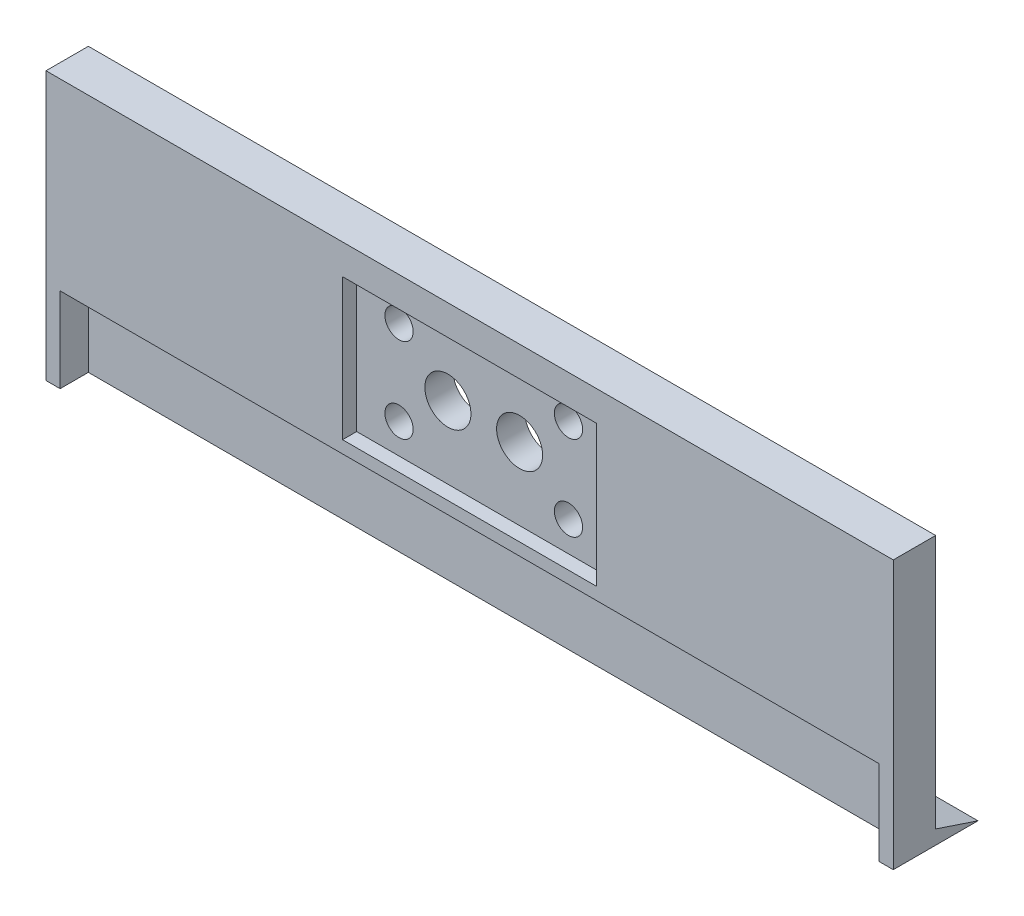
SolidWorks part; units mm, degrees
ref_plane "Plan de face" through (0, 0, 0) normal (0, 0, 1) x (1, 0, 0)
ref_plane "Plan de dessus" through (0, 0, 0) normal (0, 1, 0) x (1, 0, 0)
ref_plane "Plan de droite" through (0, 0, 0) normal (1, 0, 0) x (0, 0, -1)
sketch "Esquisse1" plane through (0, 0, 0) normal (0, 0, 1) x (1, 0, 0)
  line L1 (0, 0) -> (300, 0)
  line L2 (0, 0) -> (0, 95)
  line L3 (0, 95) -> (300, 95)
  line L4 (300, 0) -> (300, 95)
  dimension "D1" = 300
  dimension "D2" = 95
extrude "Boss.-Extru.1" add sketch "Esquisse1" along normal blind 5
sketch "Esquisse3" plane through (0, 0, 0) normal (-1, 0, 0) x (0, 0, 1)
  line L0 (0, 0) -> (-15, 0)
  line L1 (-15, 0) -> (0, 5)
  line L2 (0, 95) -> (0, 0) construction
  line L3 (0, 5) -> (0, 0)
  line M1 (0, 95) -> (0, 0)
  dimension "D1" = 15
  dimension "D2" = 5
extrude "Boss.-Extru.2" add sketch "Esquisse3" against normal up to surface (300 mm away) contours L1 L0 M1 up to face at (300, 47.5, 2.5)
sketch "Esquisse4" plane through (0, 0, 0) normal (0, 0, -1) x (-1, 0, 0)
  line L0 (-150, 95) -> (-150, -64.9747) construction
  line L1 (-300, 95) -> (0, 95) construction
  line L3 (-150, 95) -> (-195, 95)
  line L4 (-150, 95) -> (-150, 5)
  line L5 (-150, 5) -> (-195, 5)
  line L6 (-195, 95) -> (-195, 5)
  line L7 (-150, 5) -> (-105, 5)
  line L8 (-150, 5) -> (-150, 95)
  line L9 (-150, 95) -> (-105, 95)
  line L10 (-105, 5) -> (-105, 95)
  circle A0 centre (-180, 75) radius 5
  circle A1 centre (-180, 45) radius 5
  circle A2 centre (-120, 45) radius 5
  circle A3 centre (-120, 75) radius 5
  dimension "D3" = 10
  dimension "D4" = 10
  dimension "D5" = 10
  dimension "D6" = 10
  dimension "D7" = 20
  dimension "D8" = 30
  dimension "D9" = 20
  dimension "D10" = 30
  dimension "D11" = 30
  dimension "D12" = 30
  dimension "D13" = 30
  dimension "D14" = 30
  dimension "D1" = 45
  dimension "D2" = 45
  dimension "D15" = 90
sketch "Esquisse5" plane through (0, 0, 5) normal (0, 0, 1) x (1, 0, 0)
  line L0 (300, 0) -> (300, 95) construction
  line L1 (105, 95) -> (195, 95)
  line L3 (0, 0) -> (300, 0)
  line L4 (0, 0) -> (0, 95)
  line L5 (0, 0) -> (300, 0)
  line L6 (0, 0) -> (0, 30)
  line L7 (0, 95) -> (300, 95)
  line L8 (300, 0) -> (300, 30)
  line L9 (300, 0) -> (300, 95)
  line L10 (0, 95) -> (105, 95)
  line L11 (0, 95) -> (0, 30)
  line L16 (195, 95) -> (300, 95)
  line L17 (300, 30) -> (300, 95)
  line M5 (0, 95) -> (0, 0)
  line M6 (0, 0) -> (300, 0)
  line M7 (300, 0) -> (300, 95)
  line M8 (300, 95) -> (0, 95)
extrude "Boss.-Extru.3" add sketch "Esquisse5" along normal blind 10 contours L4 M8 M5 M6 M7
sketch "Esquisse6" plane through (0, 0, 0) normal (0, 0, -1) x (-1, 0, 0)
  line L0 (-150, 95) -> (-195, 95) construction
  line L1 (-150, 95) -> (-150, 5) construction
  circle A0 centre (-162.7, 60) radius 8.15
  circle A1 centre (-137.3, 60) radius 8.15
  circle A2 centre (-180, 75) radius 5
  circle A3 centre (-180, 45) radius 5
  circle A4 centre (-120, 75) radius 5
  circle A5 centre (-120, 45) radius 5
  dimension "D2" = 16.3
  dimension "D3" = 16.3
  dimension "D1" = 25.4
  dimension "D4" = 12.7
  dimension "D5" = 35
extrude "Enlèv. mat.-Extru.2" cut sketch "Esquisse6" against normal through all
sketch "Esquisse7" plane through (0, 0, 0) normal (0, -1, 0) x (1, 0, 0)
  line L0 (300, 0) -> (0, 0) construction
  line L1 (300, 15) -> (300, -15) construction
  line L2 (0, 15) -> (0, -15) construction
  line L3 (295, 28.0209) -> (5, 28.0209)
  line L4 (295, 28.0209) -> (295, 5)
  line L5 (295, 5) -> (5, 5)
  line L6 (5, 28.0209) -> (5, 5)
  dimension "D1" = 5
  dimension "D3" = 5
extrude "Enlèv. mat.-Extru.3" cut sketch "Esquisse7" against normal blind 30
sketch "Esquisse9" plane through (0, 0, 15) normal (0, 0, 1) x (1, 0, 0)
  line L0 (150, 95) -> (150, 25.265) construction
  line L1 (105, 84.3608) -> (195, 84.3608)
  line L2 (105, 84.3608) -> (105, 34.3608)
  line L3 (105, 34.3608) -> (195, 34.3608)
  line L4 (195, 84.3608) -> (195, 34.3608)
  line L5 (300, 95) -> (0, 95) construction
  dimension "D1" = 90
  dimension "D2" = 50
  dimension "D3" = 45
extrude "Enlèv. mat.-Extru.4" cut sketch "Esquisse9" against normal blind 5
